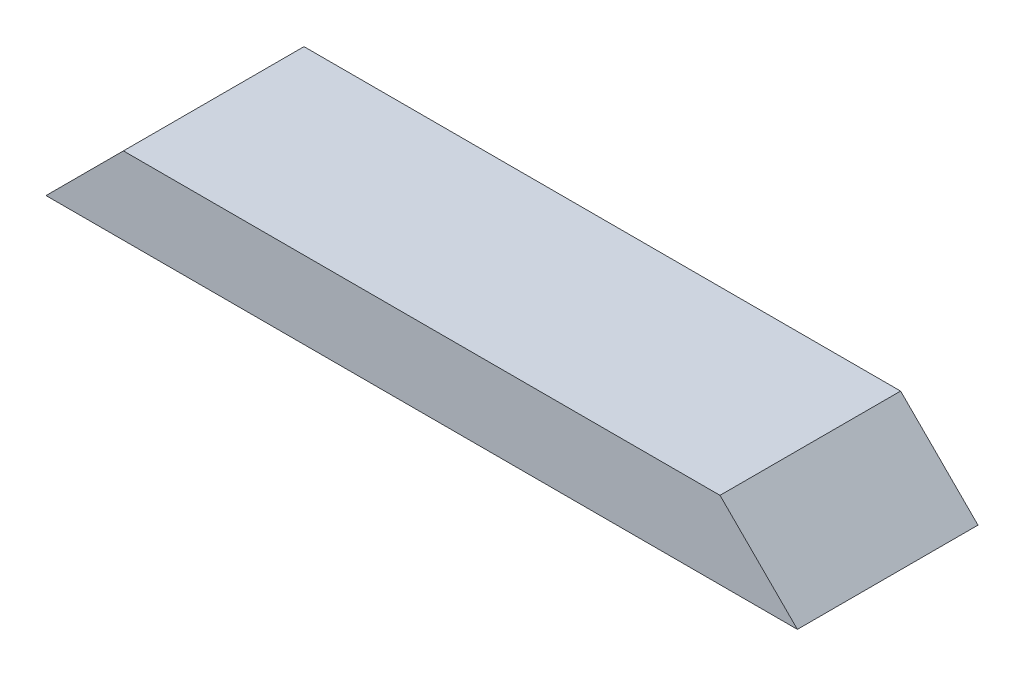
SolidWorks part; units mm, degrees
ref_plane "Front Plane" through (0, 0, 0) normal (0, 0, 1) x (1, 0, 0)
ref_plane "Top Plane" through (0, 0, 0) normal (0, 1, 0) x (1, 0, 0)
ref_plane "Right Plane" through (0, 0, 0) normal (1, 0, 0) x (0, 0, -1)
sketch "Sketch1" plane through (0, 0, 0) normal (0, 1, 0) x (1, 0, 0)
  line L1 (0, 0) -> (369.8875, 0)
  line L2 (0, 0) -> (0, 88.9)
  line L3 (0, 88.9) -> (369.8875, 88.9)
  line L4 (369.8875, 0) -> (369.8875, 88.9)
  dimension "D1" = 88.9
  dimension "D2" = 369.8875
extrude "Boss-Extrude1" add sketch "Sketch1" along normal blind 38.1
sketch "Sketch2" plane through (0, 0, 0) normal (0, 0, 1) x (1, 0, 0)
  line L0 (0, 0) -> (38.1, 38.1)
  line L1 (0, 38.1) -> (369.8875, 38.1) construction
  line L2 (38.1, 38.1) -> (0, 38.1)
  line L3 (0, 38.1) -> (0, 0)
  line L5 (369.8875, 0) -> (369.8875, 38.1)
  line L9 (369.8875, 38.1) -> (331.7875, 38.1)
  line L10 (331.7875, 38.1) -> (369.8875, 0)
  dimension "D1" = 38.1
  dimension "D2" = 38.1
  dimension "D3" = 38.1
extrude "Cut-Extrude1" cut sketch "Sketch2" against normal through all
